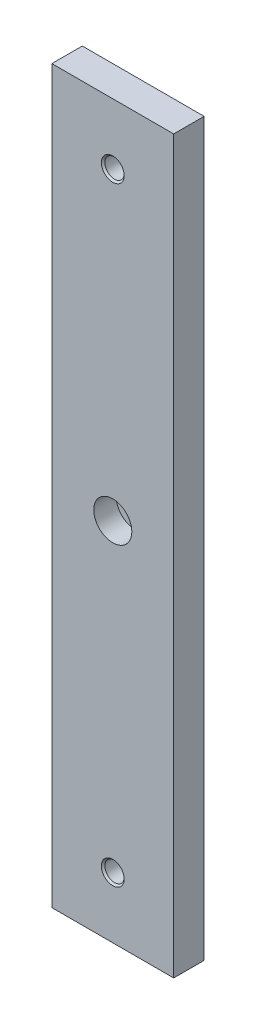
SolidWorks part; units mm, degrees
material "6061-T6 Al"
ref_plane "Front" through (0, 0, 0) normal (0, 0, 1) x (1, 0, 0)
ref_plane "Top" through (0, 0, 0) normal (0, 1, 0) x (1, 0, 0)
ref_plane "Right" through (0, 0, 0) normal (1, 0, 0) x (0, 0, -1)
sketch "Sketch1 w/mock PCB" plane through (0, 0, 0) normal (0, 0, 1) x (1, 0, 0)
  line L0 (-25.4, 152.4) -> (25.4, -152.4) construction
  line L1 (0, -127) -> (0, 127) construction
  line L2 (-25.4, 152.4) -> (25.4, 152.4)
  line L3 (-25.4, 152.4) -> (-25.4, -152.4)
  line L4 (-25.4, -152.4) -> (25.4, -152.4)
  line L6 (25.4, 152.4) -> (25.4, -152.4)
  point P5 (-25.908, 20.828)
  point P6 (25.908, 20.828)
  point P7 (25.908, -20.828)
  point P8 (-25.908, -20.828)
  point P63 (-25.781, -19.05)
  point P64 (25.781, -19.05)
  dimension "D1" = 50.8
  dimension "D2" = 304.8
  dimension "D3" = 25.4
extrude "Boss-Extrude1" add sketch "Sketch1 w/mock PCB" along normal mid plane 12.7
hole_wizard "3/8-16 Tapped Hole1" positions "Sketch2" profile "Sketch1" tap size "3/8-16" standard "ANSI Inch" end condition through all
sketch "Sketch2" plane through (0, 0, 6.35) normal (0, 0, 1) x (1, 0, 0)
  point P0 (0, -127)
  point P2 (0, 127)
sketch "Sketch1" plane through (0, -127, 6.35) normal (1, 0, 0) x (0, -1, 0)
  line L0 (0, 0) -> (0, 12.7)
  line L1 (0, 12.7) -> (4.7625, 12.7)
  line L2 (4.0322, 11.9698) -> (4.0322, 0.7302)
  line L3 (4.0322, 0.7302) -> (4.7625, 0)
  line L5 (4.7625, 0) -> (0, 0)
  line L6 (-4.0322, 0.7302) -> (-4.7625, 0) construction
  line L7 (4.7625, 12.7) -> (4.0322, 11.9698)
  line L8 (-4.7625, 12.7) -> (-4.0323, 11.9697) construction
  line L11 (0, -6.35) -> (0, 107.95) construction
  dimension "Thru Tap Drill Dia." = 8.0645
  dimension "Thru Tap Drill Depth" = 12.7
  dimension "Near C'Sink Dia." = 9.525
  dimension "Near C'Sink Angle" = 90
  dimension "Far C'Sink Dia." = 9.525
  dimension "Far C'Sink Angle" = 90
cosmetic thread "Hole Thread1" parameters "D2"=9.525
cosmetic thread "Hole Thread2" parameters "D2"=9.525
sketch "Sketch3" plane through (0, 0, 6.35) normal (0, 0, 1) x (1, 0, 0)
  circle A0 centre (0, 0) radius 7.9375
  dimension "D1" = 15.875
extrude "Cut-Extrude1" cut sketch "Sketch3" against normal blind 9.398
